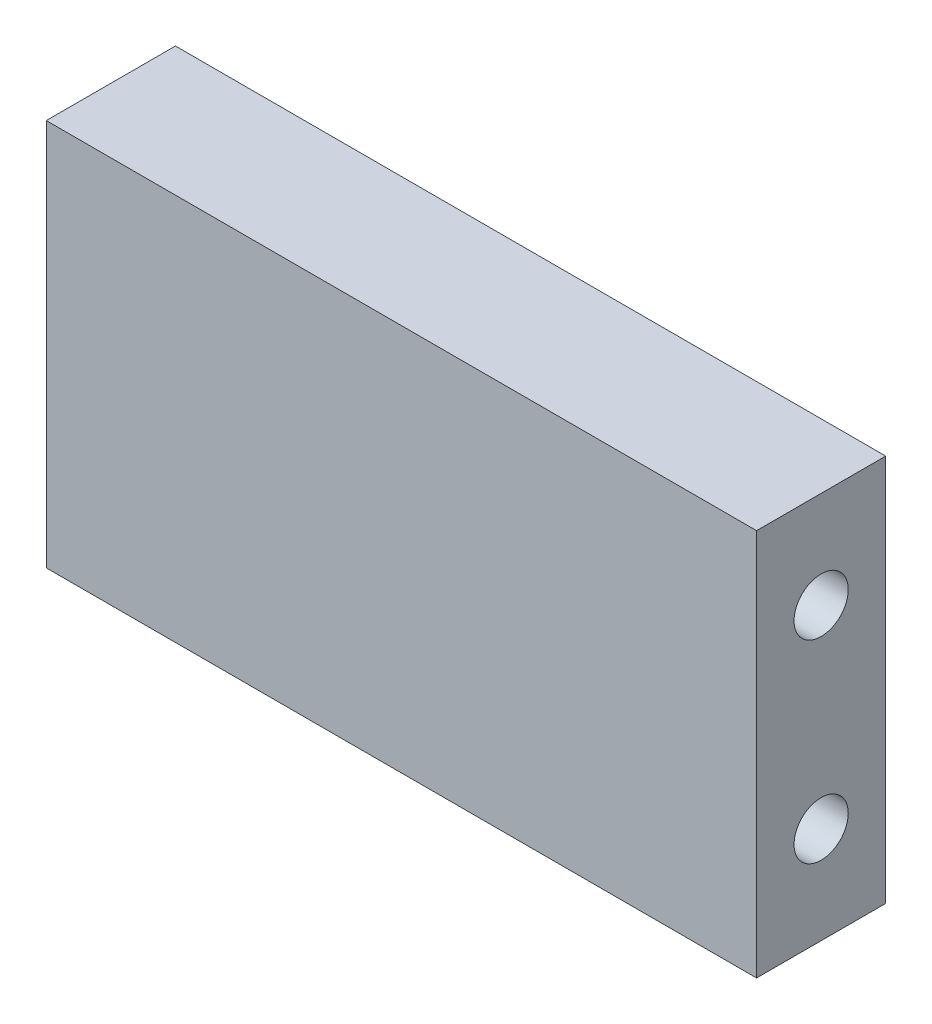
SolidWorks part; units mm, degrees
ref_plane "Front Plane" through (0, 0, 0) normal (0, 0, 1) x (1, 0, 0)
ref_plane "Top Plane" through (0, 0, 0) normal (0, 1, 0) x (1, 0, 0)
ref_plane "Right Plane" through (0, 0, 0) normal (1, 0, 0) x (0, 0, -1)
sketch "Sketch1" plane through (0, 0, 0) normal (0, 0, 1) x (1, 0, 0)
  line L1 (-27.5, -15) -> (27.5, -15)
  line L2 (-27.5, -15) -> (-27.5, 15)
  line L3 (-27.5, 15) -> (27.5, 15)
  line L4 (27.5, -15) -> (27.5, 15)
  line L5 (-27.5, -15) -> (27.5, 15) construction
  line L6 (-27.5, 15) -> (27.5, -15) construction
  point P0 (0, 0)
  dimension "D1" = 55
  dimension "D2" = 30
extrude "Boss-Extrude1" add sketch "Sketch1" along normal blind 10
sketch "Sketch2" plane through (-27.5, 0, 0) normal (-1, 0, 0) x (0, 0, 1)
  line L0 (5, 15) -> (5, -15) construction
  line L1 (10, 15) -> (0, 15) construction
  line L2 (10, -15) -> (0, -15) construction
  line L3 (5, 7.5) -> (7.9373, 7.5) construction
  line L4 (5, -7.5) -> (7.4265, -7.5) construction
  point P10 (0, 0)
  point P11 (0, 0)
  dimension "D1" = 7.5
  dimension "D2" = 15
hole_wizard "M5 Tapped Hole1" positions "3DSketch1" profile "Sketch3" tap size "M5" standard "GB"
sketch3d "3DSketch1"
  point P0 (-27.5, 7.5, 5)
  point P3 (-27.5, -7.5, 5)
sketch "Sketch3" plane through (-27.5, 7.5, 5) normal (0, 1, 0) x (0, 0, 1)
  line L0 (0, 0) -> (0, 15.2618)
  line L1 (0, 15.2618) -> (2.1, 14)
  line L2 (2.1, 14) -> (2.1, 0)
  line L5 (2.1, 0) -> (0, 0)
  line L10 (0, 15.2618) -> (-2.1, 14) construction
  line L11 (0, -6.35) -> (0, 107.95) construction
  dimension "Tap Drill Dia." = 4.2
  dimension "Tap Drill Depth" = 14
  dimension "Drill Angle" = 118
cosmetic thread "Hole Thread1" parameters "D1"=10, "D2"=5
cosmetic thread "Hole Thread2" parameters "D1"=10, "D2"=5
mirror "Mirror1" about plane through (0, 0, 0) normal (1, 0, 0) of "M5 Tapped Hole1"
cosmetic thread "Hole Thread3" parameters "D1"=10, "D2"=5
cosmetic thread "Hole Thread4" parameters "D1"=10, "D2"=5
